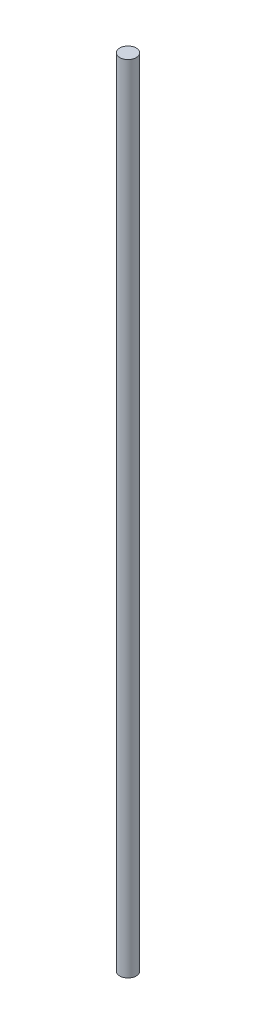
SolidWorks part; units mm, degrees
ref_plane "Front Plane" through (0, 0, 0) normal (0, 0, 1) x (1, 0, 0)
ref_plane "Top Plane" through (0, 0, 0) normal (0, 1, 0) x (1, 0, 0)
ref_plane "Right Plane" through (0, 0, 0) normal (1, 0, 0) x (0, 0, -1)
sketch "Sketch1" plane through (0, 0, 0) normal (0, 1, 0) x (1, 0, 0)
  circle A0 centre (0, 0) radius 6.35
  dimension "D1" = 12.7
extrude "Boss-Extrude1" add sketch "Sketch1" along normal blind 609.6
